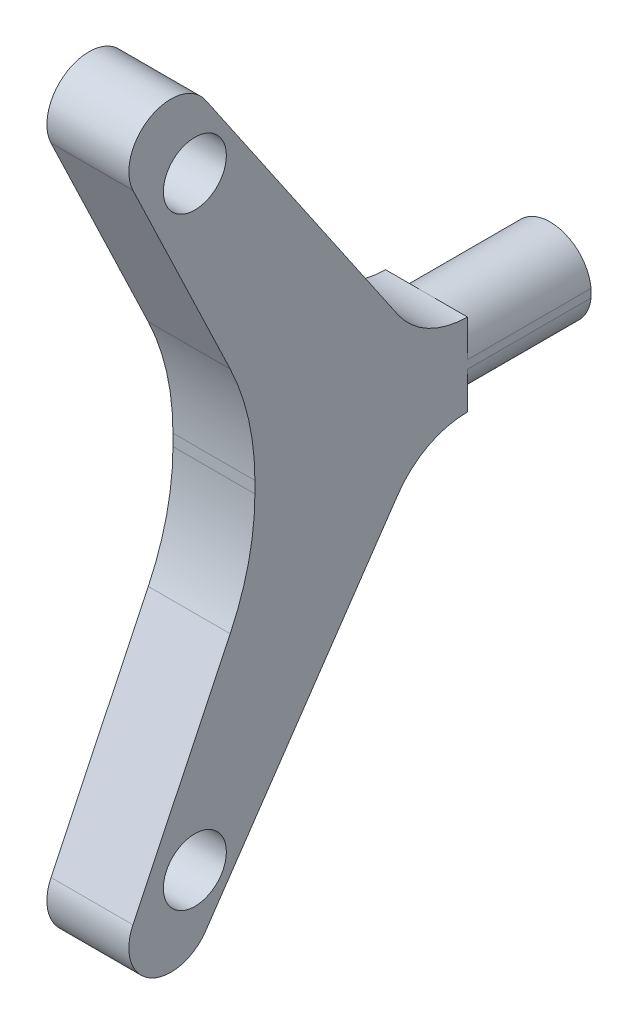
SolidWorks part; units mm, degrees
ref_plane "Front Plane" through (0, 0, 0) normal (0, 0, 1) x (1, 0, 0)
ref_plane "Top Plane" through (0, 0, 0) normal (0, 1, 0) x (1, 0, 0)
ref_plane "Right Plane" through (0, 0, 0) normal (1, 0, 0) x (0, 0, -1)
sketch "Sketch2" plane through (0, 0, 0) normal (1, 0, 0) x (0, 0, -1)
  line L0 (0, -0.6956) -> (0, 0.6956)
  line L1 (-2.9356, 13.6385) -> (-14.5107, 37.8429)
  line L2 (0, 0) -> (40, 0) construction
  line L3 (-5.8697, 42.8179) -> (17.0225, 9.2642)
  line L4 (25.2831, 4.9) -> (40, 4.9)
  line L5 (40, 4.9) -> (40, -4.9)
  line L6 (25.2831, -4.9) -> (40, -4.9)
  line L7 (-5.8697, -42.8179) -> (17.0225, -9.2642)
  line L8 (-2.9356, -13.6385) -> (-14.5107, -37.8429)
  arc A0 (-14.5107, 37.8429) -> (-5.8697, 42.8179) centre (-10, 40) cw
  arc A1 (-14.5107, -37.8429) -> (-5.8697, -42.8179) centre (-10, -40) ccw
  arc A2 (25.2831, -4.9) -> (17.0225, -9.2642) centre (25.2831, -14.9) ccw
  arc A3 (17.0225, 9.2642) -> (25.2831, 4.9) centre (25.2831, 14.9) ccw
  arc A4 (-2.9356, -13.6385) -> (0, -0.6956) centre (-30, -0.6956) ccw
  arc A5 (0, 0.6956) -> (-2.9356, 13.6385) centre (-30, 0.6956) ccw
  point P17 (20, -4.9)
  point P20 (20, 4.9)
  point P23 (0, -7.5)
  point P26 (0, 7.5)
  dimension "D2" = 5
  dimension "D8" = 10
  dimension "D9" = 30
  dimension "D1" = 40
  dimension "D3" = 40
  dimension "D4" = 20
  dimension "D5" = 10
  dimension "D6" = 7.5
  dimension "D7" = 4.9
extrude "Boss-Extrude1" add sketch "Sketch2" along normal mid plane 9.75
sketch "Sketch3" plane through (0, 0, -40) normal (0, 0, -1) x (-1, 0, 0)
  circle A0 centre (0, 0) radius 4.9
extrude "Cut-Extrude1" cut sketch "Sketch3" against normal up to vertex (14.7169 mm away) flip side to cut
sketch "Sketch4" plane through (4.875, 0, 0) normal (1, 0, 0) x (0, 0, -1)
  line L0 (-12.4948, -44.3331) -> (31.3522, 24.9092) construction
  line L1 (-12.4948, 44.3331) -> (15.5787, 0) construction
  circle A0 centre (-7.1448, 35.8846) radius 3.75
  circle A1 centre (-7.1448, -35.8846) radius 3.75
  arc A2 (-5.8697, 42.8179) -> (-14.5107, 37.8429) centre (-10, 40) ccw construction
  arc A3 (-14.5107, -37.8429) -> (-5.8697, -42.8179) centre (-10, -40) ccw construction
  point P10 (-12.4948, 44.3331)
  point P14 (-12.4948, -44.3331)
  dimension "D1" = 7.5
  dimension "D4" = 115.313
  dimension "D2" = 10
  dimension "D3" = 10
extrude "Cut-Extrude2" cut sketch "Sketch4" against normal up to vertex (9.75 mm away)
